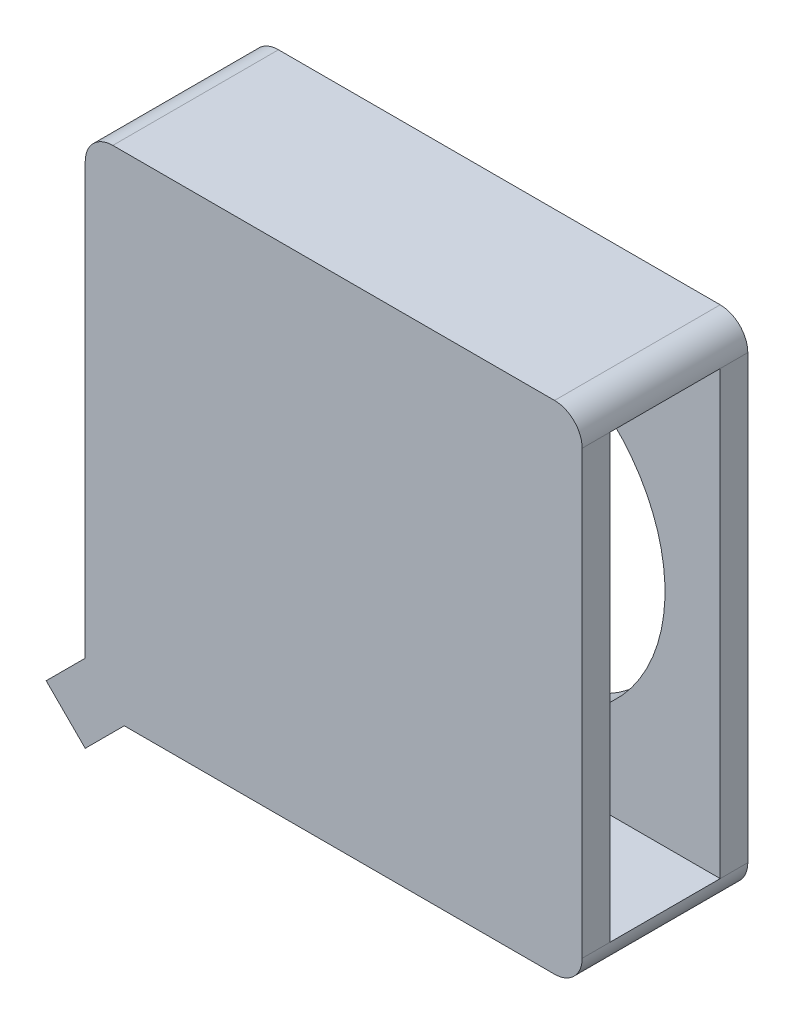
SolidWorks part; units mm, degrees
material "ABS"
ref_plane "前视基准面" through (0, 0, 0) normal (0, 0, 1) x (1, 0, 0)
ref_plane "上视基准面" through (0, 0, 0) normal (0, 1, 0) x (1, 0, 0)
ref_plane "右视基准面" through (0, 0, 0) normal (1, 0, 0) x (0, 0, -1)
sketch "草图1" plane through (0, 0, 0) normal (0, 0, 1) x (1, 0, 0)
  line L1 (-4.2159, 2.6761) -> (4.7841, 2.6761)
  line L2 (-4.2159, 2.6761) -> (-4.2159, -6.3239)
  line L3 (-4.2159, -6.3239) -> (4.7841, -6.3239)
  line L4 (4.7841, 2.6761) -> (4.7841, -6.3239)
  dimension "D1" = 9
  dimension "D2" = 9
extrude "凸台-拉伸1" add sketch "草图1" along normal blind 3
fillet "圆角1" radius 0.5 4 edges at (-4.2159, -6.3239, 1.5) (-4.2159, 2.6761, 1.5) (4.7841, -6.3239, 1.5) (4.7841, 2.6761, 1.5)
sketch "草图2" plane through (0, 0, 0) normal (0, 0, -1) x (-1, 0, 0)
  line L0 (-0.7841, 1.0015) -> (-0.7841, -5.2224) construction
  line L1 (-4.7841, -1.8239) -> (4.2159, -1.8239) construction
  line L2 (-4.7841, -5.8239) -> (-4.7841, 2.1761) construction
  line L3 (4.2159, 2.1761) -> (4.2159, -5.8239) construction
  circle A0 centre (-0.7841, -1.8239) radius 3
  point P8 (-0.7841, -1.8239)
  dimension "D2" = 6
  dimension "D1" = 4
extrude "切除-拉伸1" cut sketch "草图2" against normal blind 2.5
sketch "草图3" plane through (4.7841, 0, 0) normal (1, 0, 0) x (0, 0, -1)
  line L0 (0, -5.8239) -> (0, 2.1761) construction
  line L1 (-3, -5.8239) -> (-3, 2.1761) construction
  line L2 (0, -5.8239) -> (0, 2.1761) construction
  line L3 (-3, -5.8239) -> (-3, 2.1761) construction
  line L4 (-2.5, -5.8239) -> (-2.5, 2.1761)
  line L5 (-0.5, -5.8239) -> (-0.5, 2.1761)
  line L6 (-2.5, 2.1761) -> (-0.5, 2.1761)
  line L7 (-2.5, -5.8239) -> (-0.5, -5.8239)
  dimension "D1" = 0.5
  dimension "D2" = 0.5
extrude "切除-拉伸2" cut sketch "草图3" against normal blind 8.5
sketch "草图4" plane through (0, 0, 0) normal (0, 0, -1) x (-1, 0, 0)
  line L4 (4.2159, -5.6168) -> (3.5088, -6.3239)
  line L5 (4.2159, 2.1761) -> (4.2159, -5.8239) construction
  line L6 (3.7159, -6.3239) -> (-4.2841, -6.3239) construction
  line L7 (4.2159, -5.6168) -> (4.9231, -6.3239)
  line L8 (4.9231, -6.3239) -> (4.2159, -7.031)
  line L9 (4.2159, -7.031) -> (3.5088, -6.3239)
  dimension "D1" = 45
  dimension "D2" = 1
  dimension "D3" = 1
  dimension "D4" = 1
  dimension "D5" = 1
extrude "凸台-拉伸2" add sketch "草图4" against normal up to surface (3 mm away) up to face at (0.2841, -1.8239, 3)
